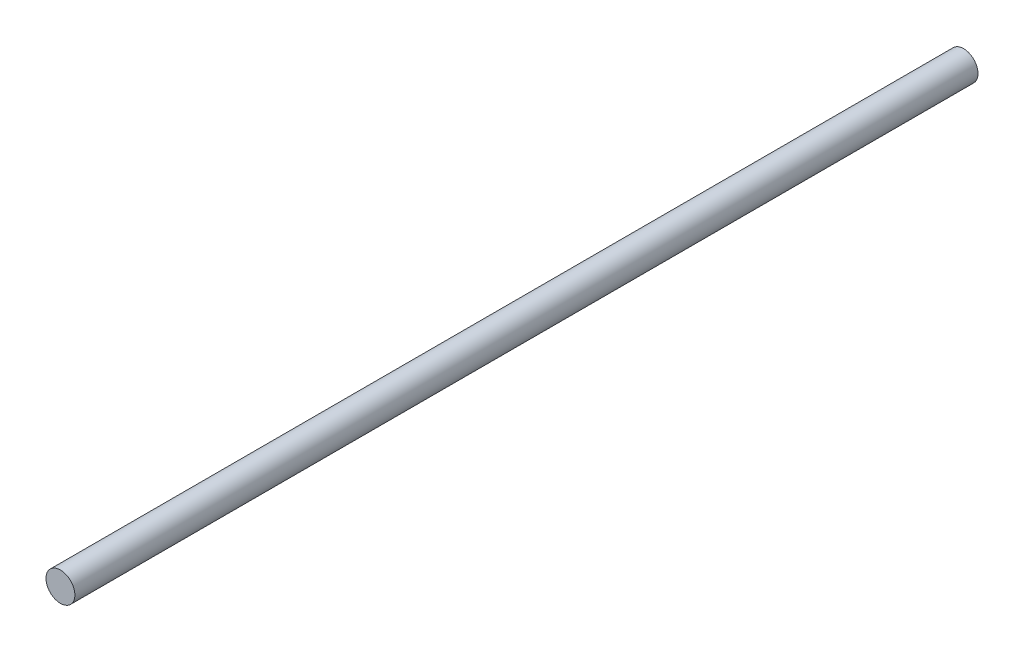
SolidWorks part; units mm, degrees
ref_plane "前视基准面" through (0, 0, 0) normal (0, 0, 1) x (1, 0, 0)
ref_plane "上视基准面" through (0, 0, 0) normal (0, 1, 0) x (1, 0, 0)
ref_plane "右视基准面" through (0, 0, 0) normal (1, 0, 0) x (0, 0, -1)
sketch "草图1" plane through (0, 0, 0) normal (0, 0, 1) x (1, 0, 0)
  circle A0 centre (0, 0) radius 6
  dimension "D1" = 12
extrude "凸台-拉伸1" add sketch "草图1" along normal blind 375
